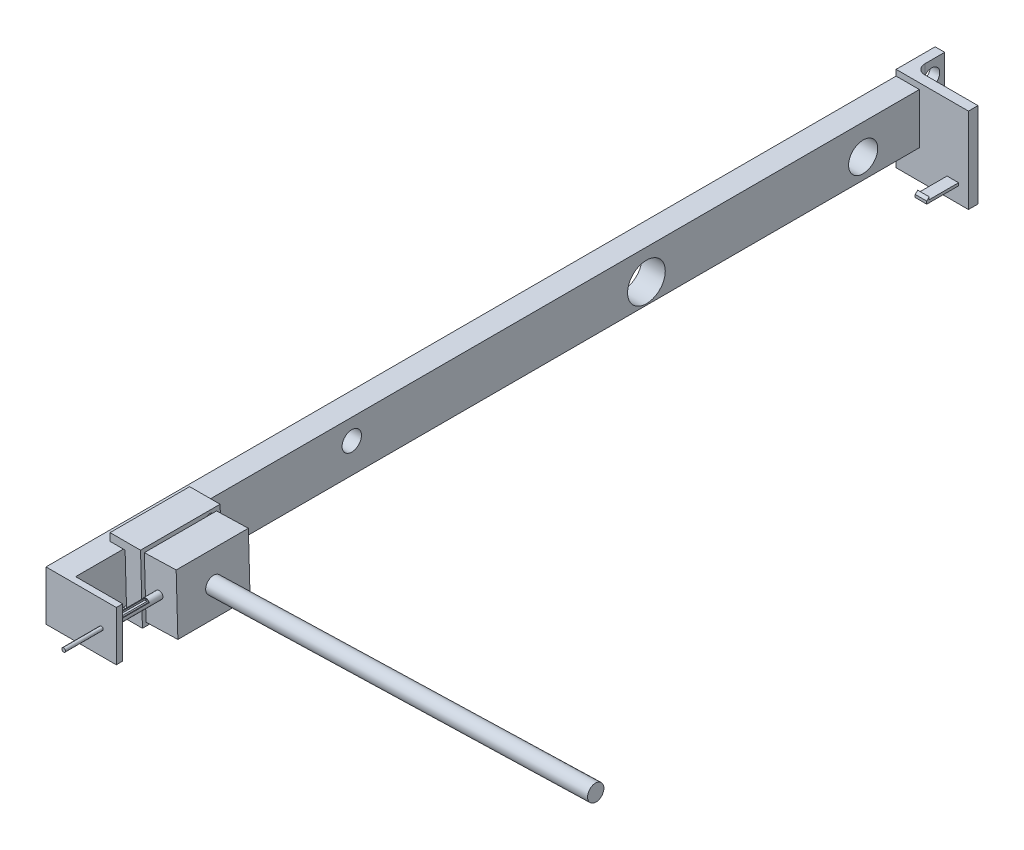
SolidWorks part; units mm, degrees
ref_plane "Front Plane" through (0, 0, 0) normal (0, 0, 1) x (1, 0, 0)
ref_plane "Top Plane" through (0, 0, 0) normal (0, 1, 0) x (1, 0, 0)
ref_plane "Right Plane" through (0, 0, 0) normal (1, 0, 0) x (0, 0, -1)
sketch "Sketch1" plane through (0, 0, 0) normal (0, 0, 1) x (1, 0, 0)
  line L1 (0, 0) -> (7.306, 0)
  line L2 (0, 0) -> (0, 15.8297)
  line L3 (0, 15.8297) -> (7.306, 15.8297)
  line L4 (7.306, 0) -> (7.306, 15.8297)
extrude "Boss-Extrude1" add sketch "Sketch1" along normal blind 250
sketch "Sketch2" plane through (7.306, 0, 0) normal (1, 0, 0) x (0, 0, -1)
  circle A0 centre (-228.5733, 9.3945) radius 2.8597
  circle A1 centre (-178.2663, 9.3945) radius 3.0436
  circle A2 centre (-85.7229, 6.3508) radius 5.9185
  circle A3 centre (-17.6604, 6.3508) radius 4.5734
extrude "Cut-Extrude1" cut sketch "Sketch2" against normal blind 250
sketch "Sketch3" plane through (0, 0, 250) normal (0, 0, 1) x (1, 0, 0)
  line L0 (3.1197, 18.2188) -> (3.1197, 15.8297)
  line L1 (7.306, 15.8297) -> (0, 15.8297) construction
  line L2 (3.1197, 15.8297) -> (7.8431, 15.8297)
  line L3 (7.8431, 15.8297) -> (8.3002, 0)
  line L4 (8.3002, 0) -> (3.1197, 0)
  line L5 (0, 0) -> (7.306, 0) construction
  line L6 (3.1197, 0) -> (3.1197, -2.7319)
  line L7 (3.1197, -2.7319) -> (13.2903, -2.7319)
  line L8 (13.2903, -2.7319) -> (12.6853, 18.2188)
  line L9 (12.6853, 18.2188) -> (3.1197, 18.2188)
extrude "Boss-Extrude2" add sketch "Sketch3" against normal blind 25
sketch "Sketch4" plane through (13.2004, 0.3812, 0) normal (0.9996, 0.0289, 0) x (0, 0, -1)
  circle A0 centre (-247.3571, 16.0041) radius 0.5563
  circle A1 centre (-228.2711, 16.0041) radius 0.9715
  circle A2 centre (-228.2711, -0.7072) radius 0.9951
  circle A3 centre (-246.8009, -0.7072) radius 0.9777
extrude "Cut-Extrude2" cut sketch "Sketch4" against normal blind 2
sketch "Sketch5" plane through (13.2004, 0.3812, 0) normal (0.9996, 0.0289, 0) x (0, 0, -1)
  line L1 (-248.835, 16.6095) -> (-226.1578, 16.6095)
  line L2 (-248.835, 16.6095) -> (-248.835, -2.041)
  line L3 (-248.835, -2.041) -> (-226.1578, -2.041)
  line L4 (-226.1578, 16.6095) -> (-226.1578, -2.041)
extrude "Boss-Extrude3" add sketch "Sketch5" along normal blind 10
sketch "Sketch7" plane through (0, 0, 250) normal (0, 0, 1) x (1, 0, 0)
  line L0 (7.306, 0) -> (7.306, 15.8297) construction
  line L1 (0, 15.8297) -> (7.306, 15.8297)
  line L2 (0, 15.8297) -> (0, 0)
  line L3 (0, 0) -> (7.306, 0)
  line L4 (7.306, 15.8297) -> (7.306, 0)
  line L5 (8.3002, 0) -> (7.306, 0) construction
extrude "Boss-Extrude4" add sketch "Sketch7" along normal blind 15
sketch "Sketch8" plane through (0, 0, 248.835) normal (0, 0, 1) x (1, 0, 0)
  circle A0 centre (17.3752, 7.8455) radius 0.5835
extrude "Boss-Extrude5" add sketch "Sketch8" along normal blind 30
sketch "Sketch10" plane through (0, 0, 248.835) normal (0, 0, 1) x (1, 0, 0)
  circle A0 centre (17.3752, 7.8455) radius 0.9911
  circle A1 centre (17.3752, 7.8455) radius 1.1761
extrude "Boss-Extrude6" add sketch "Sketch10" along normal up to surface (16.165 mm away) up to face at (3.653, 7.9148, 265)
sketch "Sketch11" plane through (0, 0, 265) normal (0, 0, 1) x (1, 0, 0)
  line L1 (0, 15.8297) -> (22.0724, 15.8297)
  line L2 (0, 15.8297) -> (0, 0.2307)
  line L3 (0, 0.2307) -> (22.0724, 0.2307)
  line L4 (22.0724, 15.8297) -> (22.0724, 0.2307)
  circle A0 centre (17.3752, 7.8455) radius 0.5835
extrude "Boss-Extrude7" add sketch "Sketch11" along normal blind 2
sketch "Sketch12" plane through (7.306, 0, 0) normal (1, 0, 0) x (0, 0, -1)
  line L0 (-248.835, 9.0216) -> (-265, 9.0216) construction
  line L1 (-261.4634, 9.0216) -> (-253.0009, 9.0216)
  line L2 (-261.4634, 9.0216) -> (-261.4634, 8.3136)
  line L3 (-261.4634, 8.3136) -> (-253.0009, 8.3136)
  line L4 (-253.0009, 9.0216) -> (-253.0009, 8.3136)
extrude "Cut-Extrude3" cut sketch "Sketch12" along normal through all
sketch "Sketch13" plane through (23.1963, 0.6698, 0) normal (0.9996, 0.0289, 0) x (0, 0, -1)
  circle A0 centre (-237.2863, 6.9246) radius 2.5581
extrude "Boss-Extrude8" add sketch "Sketch13" along normal blind 120
sketch "Sketch14" plane through (0.0589, -2.0401, 0) normal (0.0289, -0.9996, 0) x (0.9996, 0.0289, 0)
  line L1 (16.7974, 230.0466) -> (20.8341, 230.0466)
  line L2 (16.7974, 230.0466) -> (16.7974, 227.5161)
  line L3 (16.7974, 227.5161) -> (20.8341, 227.5161)
  line L4 (20.8341, 230.0466) -> (20.8341, 227.5161)
extrude "Cut-Extrude4" cut sketch "Sketch14" against normal blind 3
sketch "Sketch15" plane through (0, 0, 0) normal (0, 0, -1) x (-1, 0, 0)
  line L1 (0, 17.6701) -> (-22.7232, 17.6701)
  line L2 (0, 17.6701) -> (0, -9.1089)
  line L3 (0, -9.1089) -> (-22.7232, -9.1089)
  line L4 (-22.7232, 17.6701) -> (-22.7232, -9.1089)
extrude "Boss-Extrude9" add sketch "Sketch15" along normal blind 3
sketch "Sketch16" plane through (0, 0, 0) normal (0, 0, 1) x (1, 0, 0)
  line L1 (15.9996, -3.3604) -> (19.6224, -3.3604)
  line L2 (15.9996, -3.3604) -> (15.9996, -4.206)
  line L3 (15.9996, -4.206) -> (19.6224, -4.206)
  line L4 (19.6224, -3.3604) -> (19.6224, -4.206)
extrude "Boss-Extrude10" add sketch "Sketch16" along normal blind 10
sketch "Sketch17" plane through (19.6224, 0, 0) normal (1, 0, 0) x (0, 0, -1)
  line L0 (-10, -3.3604) -> (-9.2193, -2.5796)
  line L1 (-9.2193, -2.5796) -> (-9.2193, -3.3604)
  line L2 (-10, -3.3604) -> (0, -3.3604) construction
  line L3 (-9.2193, -3.3604) -> (-10, -3.3604)
extrude "Boss-Extrude11" add sketch "Sketch17" against normal up to surface (3.6228 mm away) up to face at (15.9996, -3.7832, 5)
sketch "Sketch20" plane through (0, 0, 0) normal (-1, 0, 0) x (0, 0, 1)
  line L1 (-3, 17.6701) -> (-12.2655, 17.6701)
  line L2 (-3, 17.6701) -> (-3, -9.1089)
  line L3 (-3, -9.1089) -> (-12.2655, -9.1089)
  line L4 (-12.2655, 17.6701) -> (-12.2655, -9.1089)
  circle A0 centre (-8.1506, 12.9159) radius 2.5552
  circle A1 centre (-7.1631, -4.8604) radius 1.646
extrude "Boss-Extrude12" add sketch "Sketch20" against normal blind 3
fillet "Fillet1" radius 3 1 edges at (3, 4.2806, -3)
